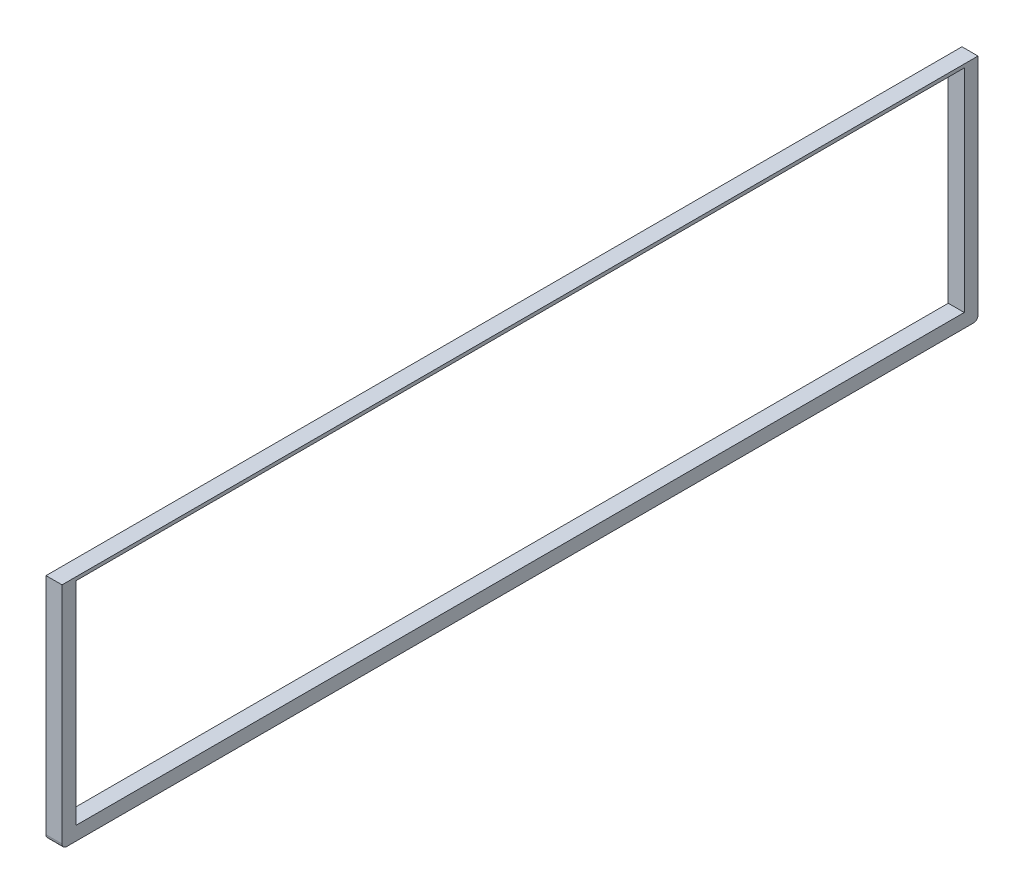
SolidWorks part; units mm, degrees
ref_plane "Front Plane" through (0, 0, 0) normal (0, 0, 1) x (1, 0, 0)
ref_plane "Top Plane" through (0, 0, 0) normal (0, 1, 0) x (1, 0, 0)
ref_plane "Right Plane" through (0, 0, 0) normal (1, 0, 0) x (0, 0, -1)
sketch "Sketch1" plane through (0, 0, 0) normal (1, 0, 0) x (0, 0, -1)
  line L1 (-1700.9859, -913.4633) -> (299.0141, -913.4633)
  line L2 (-1700.9859, -913.4633) -> (-1700.9859, -1413.4633)
  line L3 (-1700.9859, -1413.4633) -> (299.0141, -1413.4633)
  line L4 (299.0141, -913.4633) -> (299.0141, -1413.4633)
  line L5 (-1700.9859, -913.4633) -> (299.0141, -1413.4633) construction
  line L6 (-1700.9859, -1413.4633) -> (299.0141, -913.4633) construction
  point P0 (0, 0)
  dimension "D1" = 500
  dimension "D2" = 500
  dimension "D3" = 2000
extrude "Boss-Extrude1" add sketch "Sketch1" along normal blind 35
sketch "Sketch2" plane through (35, 0, 0) normal (1, 0, 0) x (0, 0, -1)
  line L0 (299.0141, -913.4633) -> (-1700.9859, -913.4633) construction
  line L3 (-1670.9859, -920.9633) -> (269.0141, -920.9633)
  line L4 (299.0141, -1413.4633) -> (299.0141, -913.4633) construction
  line L5 (-1700.9859, -913.4633) -> (-1700.9859, -1413.4633) construction
  line L6 (-1670.9859, -920.9633) -> (-1670.9859, -1383.4633)
  line L7 (-1670.9859, -1383.4633) -> (269.0141, -1383.4633)
  line L8 (269.0141, -1383.4633) -> (269.0141, -920.9633)
  line L9 (-1700.9859, -1413.4633) -> (299.0141, -1413.4633) construction
  point P4 (269.0141, -1383.4633)
  dimension "D1" = 7.5
  dimension "D2" = 30
  dimension "D3" = 30
  dimension "D4" = 30
extrude "Cut-Extrude1" cut sketch "Sketch2" against normal blind 35
fillet "Fillet1" radius 10 2 edges at (17.5, -1413.4633, -299.0141) (17.5, -1413.4633, 1700.9859)
